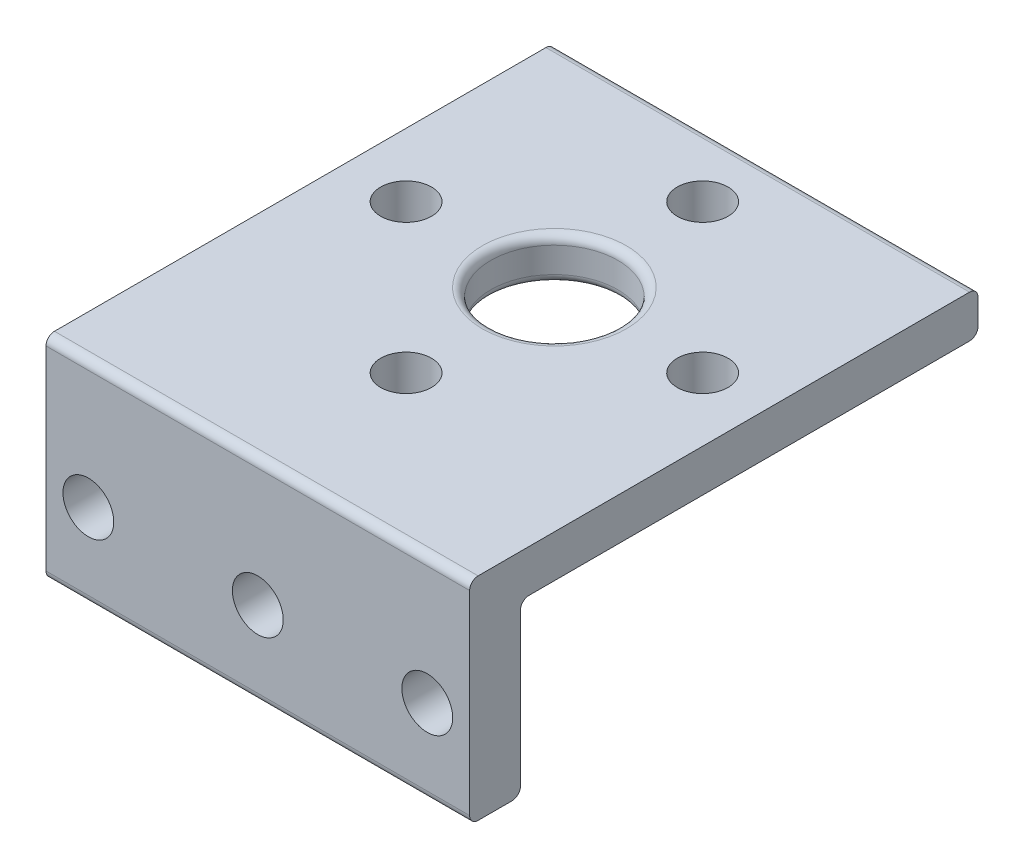
SolidWorks part; units mm, degrees
ref_plane "Front Plane" through (0, 0, 0) normal (0, 0, 1) x (1, 0, 0)
ref_plane "Top Plane" through (0, 0, 0) normal (0, 1, 0) x (1, 0, 0)
ref_plane "Right Plane" through (0, 0, 0) normal (1, 0, 0) x (0, 0, -1)
sketch "Sketch1" plane through (0, 0, 0) normal (0, 1, 0) x (1, 0, 0)
  line L1 (-25, 25) -> (25, 25)
  line L2 (-25, 25) -> (-25, -25)
  line L3 (-25, -25) -> (25, -25)
  line L4 (25, 25) -> (25, -25)
  line L5 (-25, 25) -> (25, -25) construction
  line L6 (-25, -25) -> (25, 25) construction
  circle A0 centre (0, 0) radius 7.5
  circle A1 centre (0, 17.5) radius 3
  circle A2 centre (17.5, 0) radius 3
  circle A3 centre (0, -17.5) radius 3
  circle A4 centre (-17.5, 0) radius 3
  point P0 (0, 0)
  dimension "D3" = 15
  dimension "D4" = 6
  dimension "D5" = 17.5
  dimension "D1" = 50
  dimension "D2" = 50
  dimension "D6" = 4
extrude "Boss-Extrude1" add sketch "Sketch1" along normal blind 5
sketch "Sketch2" plane through (0, 0, 25) normal (0, 0, 1) x (1, 0, 0)
  line L4 (-25, 0) -> (25, 0)
  line L5 (25, 0) -> (25, 5)
  line L6 (25, 5) -> (-25, 5)
  line L7 (-25, 5) -> (-25, 0)
  line L8 (-25, 0) -> (25, 0)
  line L9 (25, 0) -> (25, 5)
  line L10 (25, 5) -> (-25, 5)
  line L11 (-25, 5) -> (-25, 0)
  dimension "D1" = 0
extrude "Boss-Extrude2" add sketch "Sketch2" along normal blind 10
sketch "Sketch4" plane through (0, 0, 0) normal (0, -1, 0) x (1, 0, 0)
  line L0 (-25, 35) -> (25, 35)
  line L1 (25, 35) -> (25, 29)
  line L2 (25, 35) -> (25, -25) construction
  line L3 (25, 29) -> (-25, 29)
  line L4 (-25, -25) -> (-25, 35) construction
  line L5 (-25, 29) -> (-25, 35)
  dimension "D1" = 6
extrude "Boss-Extrude3" add sketch "Sketch4" along normal blind 20
sketch "Sketch5" plane through (0, 0, 29) normal (0, 0, -1) x (-1, 0, 0)
  circle A0 centre (0, -10) radius 3
  circle A1 centre (20, -10) radius 3
  circle A2 centre (-20, -10) radius 3
  dimension "D2" = 6
  dimension "D3" = 20
  dimension "D4" = 20
  dimension "D1" = 10
extrude "Cut-Extrude1" cut sketch "Sketch5" against normal through all
fillet "Fillet1" radius 1 8 edges at (0, 5, -25) (0, -20, 35) (0, 5, 7.5) (0, 0, 7.5) (0, 5, 35) (0, 0, -25) (0, -20, 29) (0, 0, 29)
